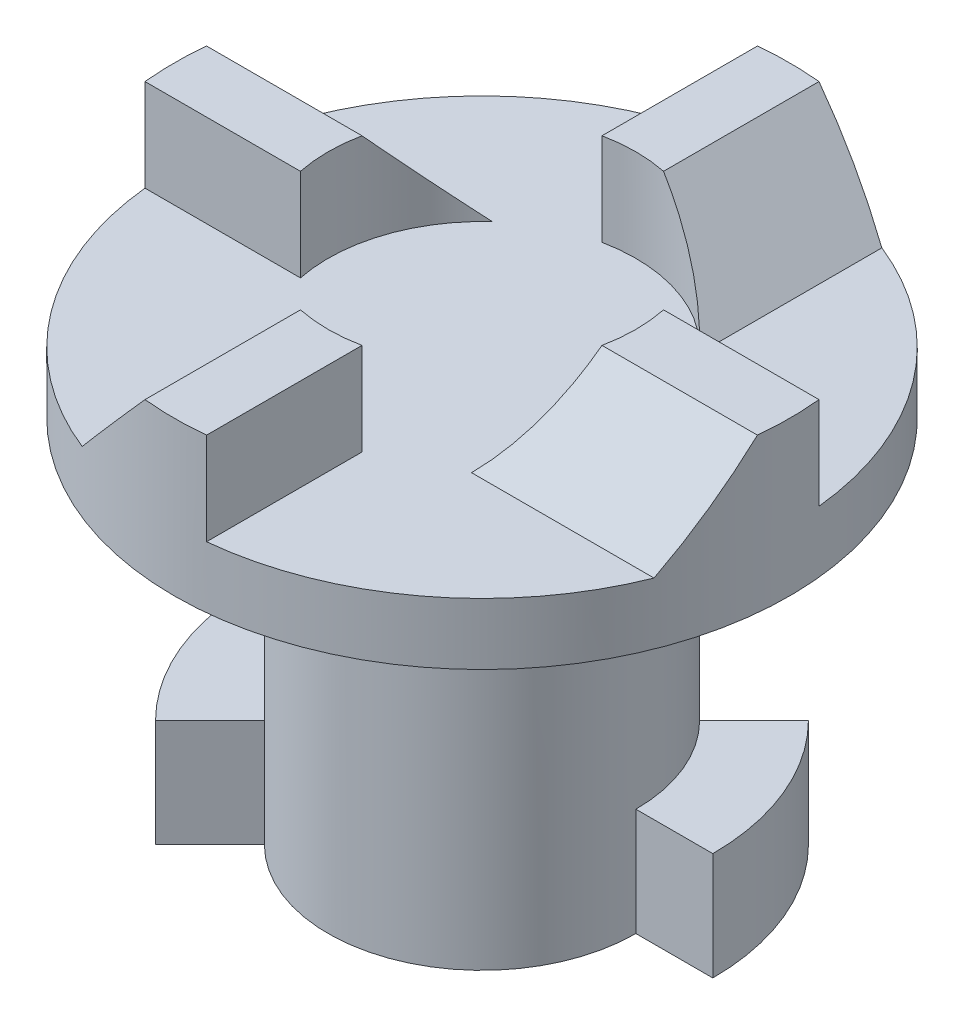
SolidWorks part; units mm, degrees
ref_plane "Front Plane" through (0, 0, 0) normal (0, 0, 1) x (1, 0, 0)
ref_plane "Top Plane" through (0, 0, 0) normal (0, 1, 0) x (1, 0, 0)
ref_plane "Right Plane" through (0, 0, 0) normal (1, 0, 0) x (0, 0, -1)
sketch "Sketch1" plane through (0, 0, 0) normal (0, 1, 0) x (1, 0, 0)
  circle A0 centre (0, 0) radius 5
  dimension "D1" = 10
extrude "Boss-Extrude1" add sketch "Sketch1" along normal blind 6
sketch "Sketch11" plane through (0, 0, 0) normal (0, -1, 0) x (1, 0, 0)
  circle A0 centre (0, 0) radius 5
  dimension "D1" = 10
extrude "Boss-Extrude5" add sketch "Sketch11" along normal blind 6
sketch "Sketch2" plane through (0, 6, 0) normal (0, 1, 0) x (1, 0, 0)
  circle A0 centre (0, 0) radius 10
  dimension "D1" = 20
extrude "Boss-Extrude2" add sketch "Sketch2" along normal blind 2
sketch "Sketch4" plane through (0, 8, 0) normal (0, 1, 0) x (1, 0, 0)
  line L1 (1, 10) -> (-1, 10)
  line L2 (1, 10) -> (1, 4.899)
  line L3 (1, -10) -> (-1, -10)
  line L4 (-1, 10) -> (-1, 4.899)
  line L7 (-10, 1) -> (-4.899, 1)
  line L8 (-10, 1) -> (-10, -1)
  line L9 (-10, -1) -> (-4.899, -1)
  line L10 (10, 1) -> (10, -1)
  line L20 (-1, -4.899) -> (-1, -10)
  line L23 (1, -4.899) -> (1, -10)
  line L24 (4.899, -1) -> (10, -1)
  line L27 (4.899, 1) -> (10, 1)
  arc A0 (-1, 4.899) -> (-4.899, 1) centre (0, 0) ccw
  arc A1 (-4.899, -1) -> (-1, -4.899) centre (0, 0) ccw
  arc A2 (4.899, 1) -> (1, 4.899) centre (0, 0) ccw
  arc A3 (1, -4.899) -> (4.899, -1) centre (0, 0) ccw
  circle A4 centre (0, 0) radius 10 construction
  point P1 (0, 10)
  point P12 (0, -10)
  point P13 (10, 0)
  point P15 (-10, 0)
  dimension "D1" = 10
  dimension "D2" = 20
  dimension "D3" = 2
extrude "Boss-Extrude3" add sketch "Sketch4" along normal blind 3
sketch "Sketch9" plane through (0, 0, -10) normal (0, 0, -1) x (-1, 0, 0)
  line L0 (-1, 11) -> (-3.7012, 8)
  line L1 (-1, 8) -> (-9.9499, 8) construction
  line L2 (-3.7012, 8) -> (-1, 8)
  line L3 (-1, 8) -> (-1, 11)
  dimension "D1" = 48
extrude "Boss-Extrude4" add sketch "Sketch9" against normal up to next
pattern_circular "CirPattern1" count 4 over 360 about axis through (0, 0, 0) along (0, 1, 0) of "Boss-Extrude4"
sketch "Sketch10" plane through (0, 8, 0) normal (0, 1, 0) x (1, 0, 0)
  circle A0 centre (0, 0) radius 10
  arc A1 (-1, 9.9499) -> (-9.2898, 3.7012) centre (0, 0) ccw construction
  circle A2 centre (0, 0) radius 13.3013
  arc M6 (9.9499, 1) -> (3.7012, 9.2898) centre (0, 0) ccw
  dimension "D1" = 26.6025
extrude "Cut-Extrude3" cut sketch "Sketch10" against normal through all both and the other way through all contours A2 A0 M6
fillet "Fillet1" radius 2 1 edges at (0, 6, 5)
sketch "Sketch12" plane through (0, 11, 0) normal (0, 1, 0) x (1, 0, 0)
  circle A0 centre (0, 0) radius 5
  dimension "D1" = 10
extrude "Cut-Extrude4" cut sketch "Sketch12" against normal up to surface (3 mm away) up to face at (-3.9017, 8, -5.8926)
sketch "Sketch14" plane through (0, -6, 0) normal (0, -1, 0) x (1, 0, 0)
  line L0 (0, 5) -> (0, 7.5)
  line L1 (-5, 0) -> (-7.5, 0)
  line L2 (0, -5) -> (0, -7.5)
  line L3 (5, 0) -> (7.5, 0)
  line L4 (-5.3033, 5.3033) -> (-3.5355, 3.5355)
  line L5 (3.5355, -3.5355) -> (5.3033, -5.3033)
  circle A0 centre (0, 0) radius 7.5
  circle A1 centre (0, 0) radius 5
  circle A2 centre (0, 0) radius 5
  circle M7 centre (0, 0) radius 5
  dimension "D2" = 15
  dimension "D3" = 45
  dimension "D4" = 45
  dimension "D1" = 0
extrude "Boss-Extrude6" add sketch "Sketch14" against normal blind 3.5 contours L4 A0 L1 M7 | L5 A0 L3 M7
